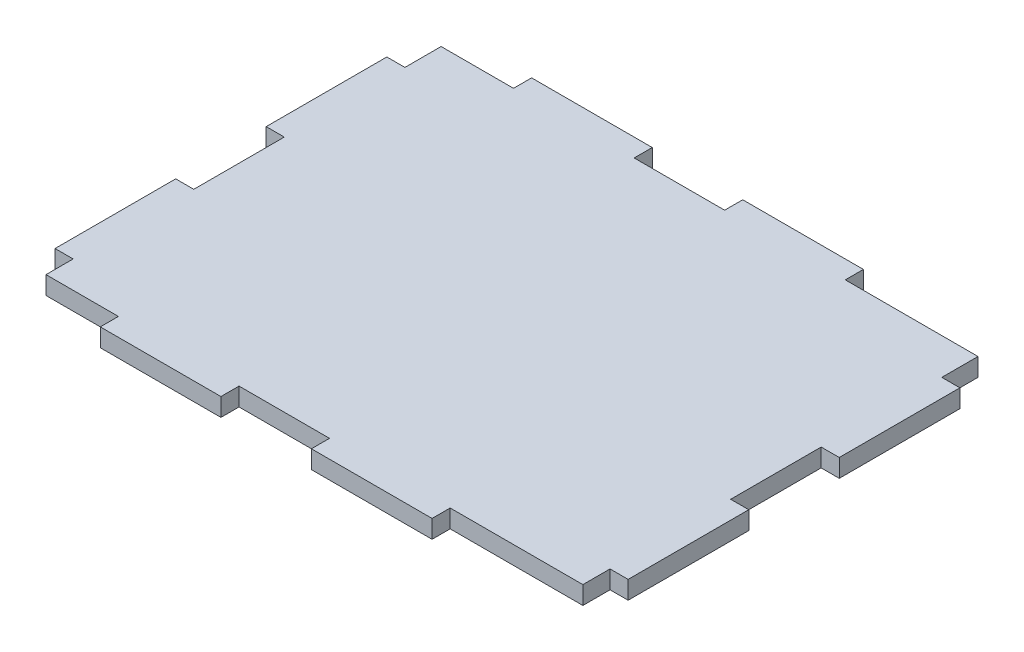
SolidWorks part; units mm, degrees
ref_plane "Front Plane" through (0, 0, 0) normal (0, 0, 1) x (1, 0, 0)
ref_plane "Top Plane" through (0, 0, 0) normal (0, 1, 0) x (1, 0, 0)
ref_plane "Right Plane" through (0, 0, 0) normal (1, 0, 0) x (0, 0, -1)
sketch "Sketch1" plane through (0, 0, 0) normal (0, 1, 0) x (1, 0, 0)
  line L0 (12, 65.5) -> (0, 65.5)
  line L1 (89, 0) -> (67, 0)
  line L2 (89, 0) -> (89, 4.5)
  line L3 (89, 65.5) -> (67, 65.5)
  line L4 (0, 0) -> (0, 4.5)
  line L5 (47, 65.5) -> (32, 65.5)
  line L6 (12, 65.5) -> (12, 68.5)
  line L7 (12, 68.5) -> (32, 68.5)
  line L8 (32, 65.5) -> (32, 68.5)
  line L11 (89, 59.5) -> (89, 65.5)
  line L12 (47, 65.5) -> (47, 68.5)
  line L13 (47, 68.5) -> (67, 68.5)
  line L14 (67, 65.5) -> (67, 68.5)
  line L17 (0, 59.5) -> (-3, 59.5)
  line L19 (0, 24.5) -> (-3, 24.5)
  line L20 (-3, 59.5) -> (-3, 39.5)
  line L23 (0, 39.5) -> (-3, 39.5)
  line L24 (0, 59.5) -> (0, 65.5)
  line L25 (0, 4.5) -> (-3, 4.5)
  line L26 (-3, 24.5) -> (-3, 4.5)
  line L29 (0, 39.5) -> (0, 24.5)
  line L30 (12, 0) -> (12, -3)
  line L31 (12, -3) -> (32, -3)
  line L32 (32, 0) -> (32, -3)
  line L35 (12, 0) -> (0, 0)
  line L36 (47, 0) -> (47, -3)
  line L37 (47, -3) -> (67, -3)
  line L38 (67, 0) -> (67, -3)
  line L41 (89, 4.5) -> (92, 4.5)
  line L42 (47, 0) -> (32, 0)
  line L43 (89, 39.5) -> (92, 39.5)
  line L44 (92, 4.5) -> (92, 24.5)
  line L47 (89, 59.5) -> (92, 59.5)
  line L48 (89, 39.5) -> (89, 24.5)
  line L49 (89, 24.5) -> (92, 24.5)
  line L50 (92, 59.5) -> (92, 39.5)
  point P14 (0, 0)
  point P19 (0, 0)
  dimension "D1" = 20
  dimension "D2" = 89
  dimension "D3" = 65.5
  dimension "D4" = 3
  dimension "D5" = 6
  dimension "D6" = 15
  dimension "D7" = 12
extrude "Boss-Extrude1" add sketch "Sketch1" along normal blind 3
